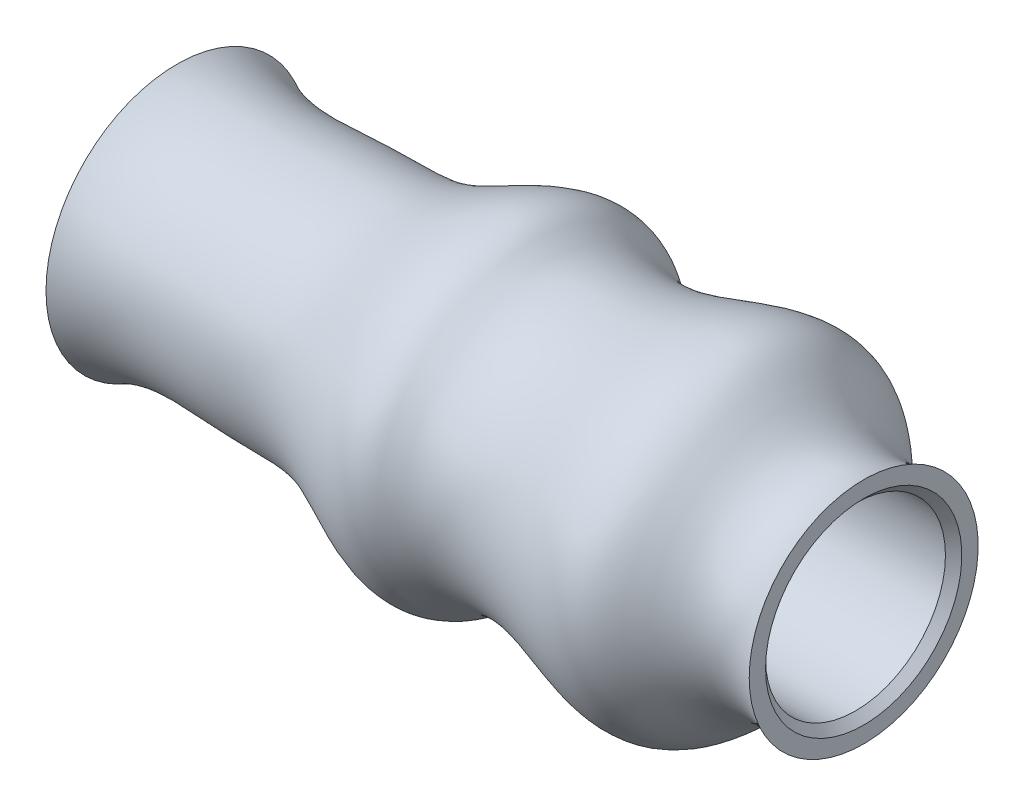
SolidWorks part; units mm, degrees
ref_plane "Face" through (0, 0, 0) normal (0, 0, 1) x (1, 0, 0)
ref_plane "Dessus" through (0, 0, 0) normal (0, 1, 0) x (1, 0, 0)
ref_plane "Droite" through (0, 0, 0) normal (1, 0, 0) x (0, 0, -1)
sketch "Esquisse1" plane through (0, 0, 0) normal (0, 0, 1) x (1, 0, 0)
  line L0 (-84.2135, 0) -> (96.0192, 0) construction
  line L1 (0, 7.2284) -> (0, 8)
  line L5 (42, 7) -> (42, 5.5)
  line L6 (42, 5.5) -> (7, 5.5)
  line L7 (7, 5.5) -> (7, 2.5)
  line L8 (7, 2.5) -> (5.0711, 2.5)
  arc A0 (5.0711, 2.5) -> (0, 7.2284) centre (-2, 0) ccw
  spline S0 degree 3 poles (0, 8) (2.7105, 6.5713) (7.5541, 7.4099) (14.4907, 6.911) (19.7584, 11.1639) (23.6284, 7.9581) (28.5117, 8.5302) (35.8015, 11.9082) (38.3378, 5.1752) (42, 7) knots 0 0 0 0 0.20761 0.324503 0.503256 0.537353 0.665473 0.817129 1 1 1 1
  dimension "D9" = 15
  dimension "D10" = 2
  dimension "D1" = 5
  dimension "D2" = 11
  dimension "D7" = 42
  dimension "D8" = 35
revolve "Base-Révolution" add sketch "Esquisse1" angle 360 about L0
cosmetic thread "Représentation de filetage1" parameters "D1"=8, "D2"=12
ref_plane "Plan1" through (4, 0, 0) normal (-1, 0, 0) x (0, 0, 1)
chamfer "Chanfrein4" distance 0.5 angle 45 1 edges at (42, 0, 5.5)
